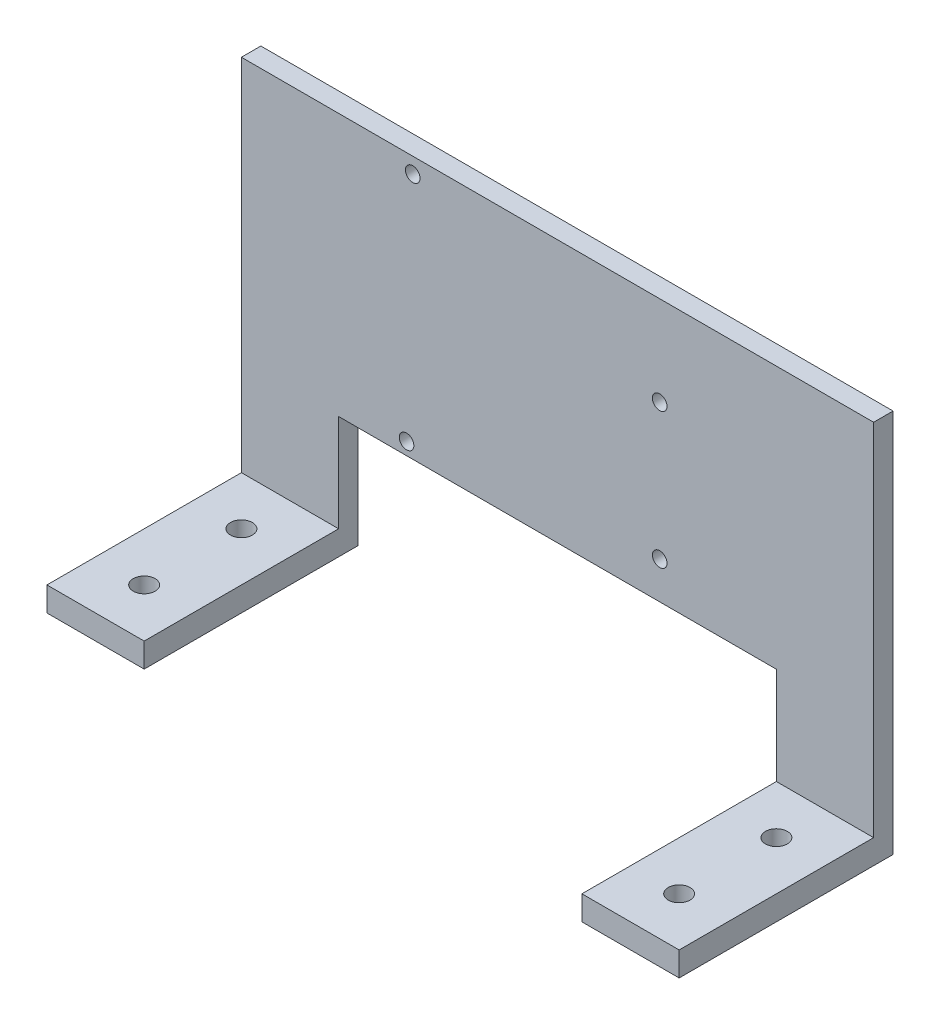
SolidWorks part; units mm, degrees
ref_plane "Front Plane" through (0, 0, 0) normal (0, 0, 1) x (1, 0, 0)
ref_plane "Top Plane" through (0, 0, 0) normal (0, 1, 0) x (1, 0, 0)
ref_plane "Right Plane" through (0, 0, 0) normal (1, 0, 0) x (0, 0, -1)
sketch "Sketch1" plane through (0, 0, 0) normal (0, 1, 0) x (1, 0, 0)
  line L1 (-10, 34) -> (10, 34)
  line L2 (-10, 34) -> (-10, -10)
  line L3 (-10, -10) -> (10, -10)
  line L4 (10, 34) -> (10, -10)
  line L5 (100.04, 34) -> (120.04, 34)
  line L6 (100.04, 34) -> (100.04, -10)
  line L7 (100.04, -10) -> (120.04, -10)
  line L8 (120.04, 34) -> (120.04, -10)
  circle A0 centre (0, 0) radius 2.25
  circle A1 centre (0, 20) radius 2.25
  circle A2 centre (110.04, 20) radius 2.25
  circle A3 centre (110.04, 0) radius 2.25
  dimension "D1" = 4.5
  dimension "D2" = 20
  dimension "D3" = 110.04
  dimension "D4" = 10
  dimension "D5" = 20
  dimension "D6" = 14
  dimension "D7" = 44
  dimension "D8" = 44
  dimension "D9" = 20
  dimension "D10" = 10
  dimension "D11" = 14
extrude "Boss-Extrude1" add sketch "Sketch1" along normal blind 5
sketch "Sketch2" plane through (0, 5, 0) normal (0, 1, 0) x (1, 0, 0)
  line L0 (120.04, -10) -> (120.04, 34) construction
  line L1 (-10, 34) -> (120.04, 34)
  line L2 (-10, 34) -> (-10, 30)
  line L3 (-10, 30) -> (120.04, 30)
  line L4 (120.04, 34) -> (120.04, 30)
  dimension "D1" = 4
extrude "Boss-Extrude2" add sketch "Sketch2" along normal blind 74 and the other way blind 5
sketch "Sketch3" plane through (0, 0, -30) normal (0, 0, 1) x (1, 0, 0)
  line L1 (10, 0) -> (100.04, 0)
  line L2 (10, 0) -> (10, 25)
  line L3 (10, 25) -> (100.04, 25)
  line L4 (100.04, 0) -> (100.04, 25)
  point P5 (0, 0)
  dimension "D1" = 25
extrude "Cut-Extrude1" cut sketch "Sketch3" against normal blind 5
hole_wizard "Ø3.0mm Dowel Hole1" positions "Sketch4" profile "Sketch5" hole size "Ø3.0" standard "IS"
sketch "Sketch4" plane through (55.8344, -56, -30) normal (0, 0, 1) x (1, 0, 0)
  point P0 (-30.5944, 131.8)
  point P3 (20.2056, 116.56)
  point P6 (20.2056, 88.62)
  point P9 (-31.8644, 83.54)
sketch "Sketch5" plane through (25.24, 75.8, -30) normal (1, 0, 0) x (0, -1, 0)
  line L0 (0, 0) -> (0, 5.9013)
  line L1 (0, 5.9013) -> (1.5, 5)
  line L2 (1.5, 5) -> (1.5, 0)
  line L3 (1.5, 0) -> (0, 0)
  line L4 (0, 5.9013) -> (-1.5, 5) construction
  line L5 (0, -6.35) -> (0, 107.95) construction
  dimension "Hole Dia." = 3
  dimension "Hole Depth" = 5
  dimension "Drill Angle" = 118
